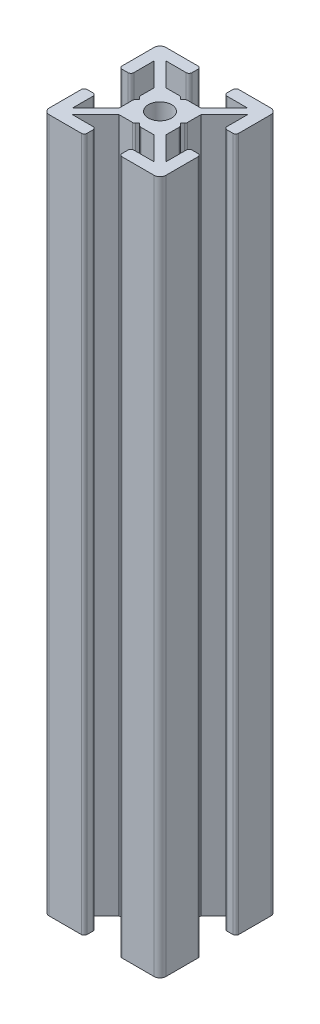
SolidWorks part; units mm, degrees
ref_plane "Front Plane" through (0, 0, 0) normal (0, 0, 1) x (1, 0, 0)
ref_plane "Top Plane" through (0, 0, 0) normal (0, 1, 0) x (1, 0, 0)
ref_plane "Right Plane" through (0, 0, 0) normal (1, 0, 0) x (0, 0, -1)
sketch "Sketch1" plane through (0, 0, 0) normal (0, 1, 0) x (1, 0, 0)
  line L0 (7, 20) -> (7, 18)
  line L1 (0, 0) -> (20, 0)
  line L2 (0, 0) -> (0, 20)
  line L3 (0, 20) -> (20, 20)
  line L4 (20, 0) -> (20, 20)
  line L5 (7, 18) -> (3, 18)
  line L6 (3, 18) -> (7, 14)
  line L7 (7, 14) -> (13, 14)
  line L8 (13, 14) -> (17, 18)
  line L9 (17, 18) -> (13, 18)
  line L10 (13, 18) -> (13, 20)
  line L11 (13, 20) -> (7, 20)
  line L12 (20, 7) -> (20, 13)
  line L13 (20, 13) -> (18, 13)
  line L14 (18, 13) -> (18, 17)
  line L15 (18, 17) -> (14, 13)
  line L16 (14, 13) -> (14, 7)
  line L17 (14, 7) -> (18, 3)
  line L18 (18, 3) -> (18, 7)
  line L19 (18, 7) -> (20, 7)
  line L20 (7, 0) -> (13, 0)
  line L21 (13, 0) -> (13, 2)
  line L22 (13, 2) -> (17, 2)
  line L23 (17, 2) -> (13, 6)
  line L24 (13, 6) -> (7, 6)
  line L25 (7, 6) -> (3, 2)
  line L26 (3, 2) -> (7, 2)
  line L27 (7, 2) -> (7, 0)
  line L28 (0, 13) -> (0, 7)
  line L29 (0, 7) -> (2, 7)
  line L30 (2, 7) -> (2, 3)
  line L31 (2, 3) -> (6, 7)
  line L32 (6, 7) -> (6, 13)
  line L33 (6, 13) -> (2, 17)
  line L34 (2, 17) -> (2, 13)
  line L35 (2, 13) -> (0, 13)
  line L36 (9.5, 14) -> (10.5, 14)
  line L37 (10.5, 14) -> (10, 13.5)
  line L38 (10, 13.5) -> (9.5, 14)
  line L39 (13.5, 10) -> (14, 10.5)
  line L40 (14, 10.5) -> (14, 9.5)
  line L41 (14, 9.5) -> (13.5, 10)
  line L42 (10, 6.5) -> (10.5, 6)
  line L43 (10.5, 6) -> (9.5, 6)
  line L44 (9.5, 6) -> (10, 6.5)
  line L45 (6.5, 10) -> (6, 9.5)
  line L46 (6, 9.5) -> (6, 10.5)
  line L47 (6, 10.5) -> (6.5, 10)
  circle A0 centre (10, 10) radius 2
  point P10 (10, 10)
  point P41 (10, 10)
  point P43 (10, 14)
  point P57 (10, 10)
  dimension "D8" = 4
  dimension "D1" = 20
  dimension "D2" = 20
  dimension "D3" = 7
  dimension "D4" = 7
  dimension "D5" = 6
  dimension "D6" = 4
  dimension "D7" = 4
  dimension "D9" = 0.5
  dimension "D11" = 0.5
  dimension "D12" = 0.5
  dimension "D13" = 4
  dimension "D10" = 4
extrude "Boss-Extrude1" add sketch "Sketch1" along normal blind 119 contours L35 L34 L33 L32 L31 L30 L29 L2 L1 L27 L26 L25 L24 L23 L22 L21 L4 L19 L18 L17 L16 L15 L14 L13 L3 L10 L9 L8 L7 L6 L5 L0 A0
fillet "Fillet1" radius 1 4 edges at (0, 59.5, -20) (0, 59.5, 0) (20, 59.5, 0) (20, 59.5, -20)
fillet "Fillet2" radius 0.5 16 edges at (20, 59.5, -13) (18, 59.5, -13) (20, 59.5, -7) (18, 59.5, -7) (13, 59.5, -2) (13, 59.5, 0) (7, 59.5, 0) (7, 59.5, -2) (0, 59.5, -7) (2, 59.5, -7) (13, 59.5, -20) (13, 59.5, -18) (7, 59.5, -20) (7, 59.5, -18) (0, 59.5, -13) (2, 59.5, -13)
fillet "Fillet4" radius 0.5 8 edges at (10.5, 59.5, -6) (9.5, 59.5, -6) (6, 59.5, -9.5) (6, 59.5, -10.5) (10.5, 59.5, -14) (9.5, 59.5, -14) (14, 59.5, -9.5) (14, 59.5, -10.5)
